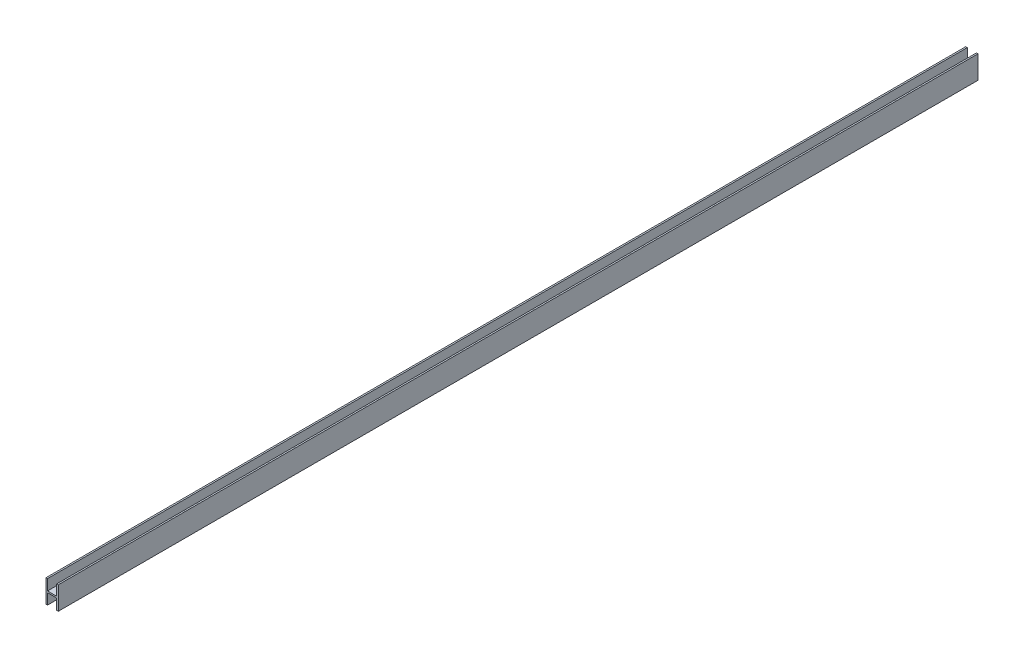
SolidWorks part; units mm, degrees
material "6063-T5"
ref_plane "前视基准面" through (0, 0, 0) normal (0, 0, 1) x (1, 0, 0)
ref_plane "上视基准面" through (0, 0, 0) normal (0, 1, 0) x (1, 0, 0)
ref_plane "右视基准面" through (0, 0, 0) normal (1, 0, 0) x (0, 0, -1)
sketch "草图1" plane through (0, 0, 0) normal (0, 0, 1) x (1, 0, 0)
  line L1 (-4, -7.5) -> (4, -7.5)
  line L2 (-4, -7.5) -> (-4, 7.5)
  line L3 (-4, 7.5) -> (4, 7.5)
  line L4 (4, -7.5) -> (4, 7.5)
  line L5 (-4, -7.5) -> (4, 7.5) construction
  line L6 (-4, 7.5) -> (4, -7.5) construction
  point P0 (0, 0)
  dimension "D1" = 15
  dimension "D2" = 8
extrude "凸台-拉伸1" add sketch "草图1" along normal blind 600
sketch "草图2" plane through (0, 0, 0) normal (0, 0, -1) x (-1, 0, 0)
  line L0 (4, -7.5) -> (-4, -7.5) construction
  line L1 (-3, -14.5) -> (3, -14.5)
  line L2 (-3, -14.5) -> (-3, -0.5)
  line L3 (-3, -0.5) -> (3, -0.5)
  line L4 (3, -14.5) -> (3, -0.5)
  line L5 (-3, -14.5) -> (3, -0.5) construction
  line L6 (-3, -0.5) -> (3, -14.5) construction
  line L7 (-4, 7.5) -> (4, 7.5) construction
  line L8 (-3, 0.5) -> (3, 0.5)
  line L9 (-3, 0.5) -> (-3, 14.5)
  line L10 (-3, 14.5) -> (3, 14.5)
  line L11 (3, 0.5) -> (3, 14.5)
  line L12 (-3, 0.5) -> (3, 14.5) construction
  line L13 (-3, 14.5) -> (3, 0.5) construction
  point P0 (0, -7.5)
  point P7 (0, 7.5)
  dimension "D1" = 6
  dimension "D2" = 6
  dimension "D3" = 0.5
  dimension "D4" = 0.5
extrude "切除-拉伸1" cut sketch "草图2" against normal blind 2400
